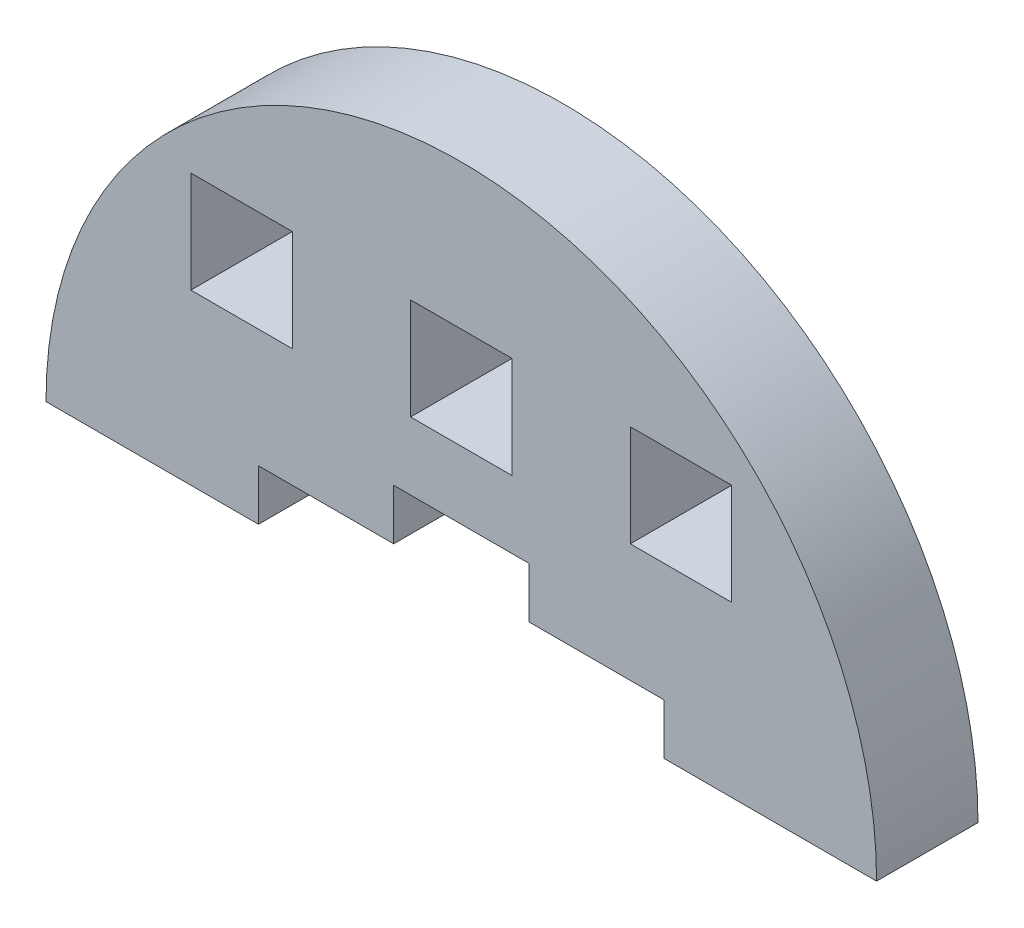
SolidWorks part; units mm, degrees
ref_plane "Front Plane" through (0, 0, 0) normal (0, 0, 1) x (1, 0, 0)
ref_plane "Top Plane" through (0, 0, 0) normal (0, 1, 0) x (1, 0, 0)
ref_plane "Right Plane" through (0, 0, 0) normal (1, 0, 0) x (0, 0, -1)
sketch "Model" plane through (0, 0, 0) normal (0, 0, 1) x (1, 0, 0)
  line L0 (3736.9541, 1243.7818) -> (3749.5256, 1243.7818)
  line L1 (3773.5256, 1243.7818) -> (3786.097, 1243.7818)
  line L2 (3765.5256, 1246.7818) -> (3773.5256, 1246.7818)
  line L3 (3773.5256, 1246.7818) -> (3773.5256, 1243.7818)
  line L4 (3757.5256, 1246.7818) -> (3749.5256, 1246.7818)
  line L5 (3749.5256, 1246.7818) -> (3749.5256, 1243.7818)
  line L6 (3771.5256, 1259.7818) -> (3777.5256, 1259.7818)
  line L7 (3777.5256, 1259.7818) -> (3777.5256, 1253.7818)
  line L8 (3777.5256, 1253.7818) -> (3771.5256, 1253.7818)
  line L9 (3771.5256, 1253.7818) -> (3771.5256, 1259.7818)
  line L10 (3751.5256, 1259.7818) -> (3745.5256, 1259.7818)
  line L11 (3745.5256, 1259.7818) -> (3745.5256, 1253.7818)
  line L12 (3745.5256, 1253.7818) -> (3751.5256, 1253.7818)
  line L13 (3751.5256, 1253.7818) -> (3751.5256, 1259.7818)
  line L14 (3764.5256, 1259.7818) -> (3758.5256, 1259.7818)
  line L15 (3758.5256, 1259.7818) -> (3758.5256, 1253.7818)
  line L16 (3758.5256, 1253.7818) -> (3764.5256, 1253.7818)
  line L17 (3764.5256, 1253.7818) -> (3764.5256, 1259.7818)
  line L18 (3757.5256, 1249.7818) -> (3757.5256, 1246.7818)
  line L19 (3757.5256, 1249.7818) -> (3765.5256, 1249.7818)
  line L20 (3765.5256, 1249.7818) -> (3765.5256, 1246.7818)
  arc A0 (3786.097, 1243.7818) -> (3736.9541, 1243.7818) centre (3761.5256, 1243.7818) ccw
extrude "Boss-Extrude1" add sketch "Model" along normal blind 6 contours L12 L13 L10 L11 | L9 L8 L7 L6 | A0 L0 L5 L4 L18 L19 L20 L2 L3 L1 | L15 L16 L17 L14
